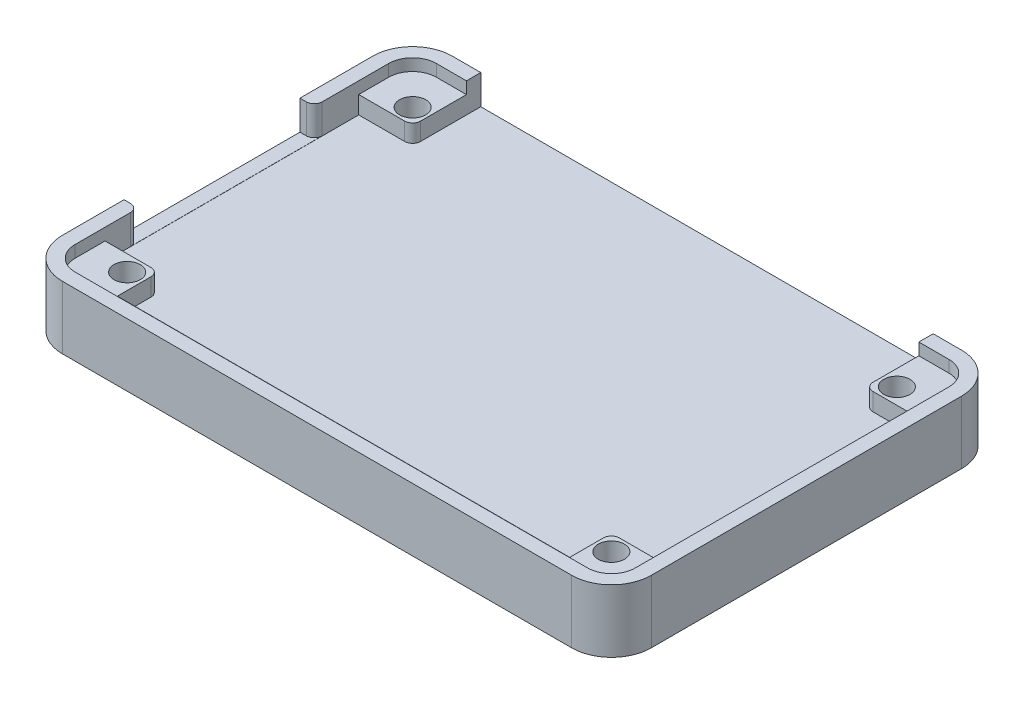
SolidWorks part; units mm, degrees
ref_plane "Front Plane" through (0, 0, 0) normal (0, 0, 1) x (1, 0, 0)
ref_plane "Top Plane" through (0, 0, 0) normal (0, 1, 0) x (1, 0, 0)
ref_plane "Right Plane" through (0, 0, 0) normal (1, 0, 0) x (0, 0, -1)
sketch "Sketch1" plane through (0, 0, 0) normal (0, 1, 0) x (1, 0, 0)
  line L1 (-37, -24.5) -> (37, -24.5)
  line L2 (-37, -24.5) -> (-37, 24.5)
  line L3 (-37, 24.5) -> (37, 24.5)
  line L4 (37, -24.5) -> (37, 24.5)
  line L5 (-37, -24.5) -> (37, 24.5) construction
  line L6 (-37, 24.5) -> (37, -24.5) construction
  point P0 (0, 0)
  dimension "D1" = 74
  dimension "D2" = 49
extrude "Boss-Extrude1" add sketch "Sketch1" along normal blind 7.9
sketch "Sketch3" plane through (0, 7.9, 0) normal (0, 1, 0) x (1, 0, 0)
  line L1 (-30.424, -17.9375) -> (30.424, -17.9375) construction
  line L2 (-30.424, -17.9375) -> (-30.424, 17.9375) construction
  line L3 (-30.424, 17.9375) -> (30.424, 17.9375) construction
  line L4 (30.424, -17.9375) -> (30.424, 17.9375) construction
  line L5 (-30.424, -17.9375) -> (30.424, 17.9375) construction
  line L6 (-30.424, 17.9375) -> (30.424, -17.9375) construction
  circle A0 centre (-30.424, 17.9375) radius 1.65
  circle A1 centre (30.424, 17.9375) radius 1.65
  circle A2 centre (-30.424, -17.9375) radius 1.65
  circle A3 centre (30.424, -17.9375) radius 1.65
  point P0 (0, 0)
  dimension "D3" = 3.3
  dimension "D4" = 3.3
  dimension "D5" = 3.3
  dimension "D6" = 3.3
  dimension "D1" = 60.848
  dimension "D2" = 35.875
fillet "Fillet1" radius 5 4 edges at (-37, 3.95, 24.5) (-37, 3.95, -24.5) (37, 3.95, 24.5) (37, 3.95, -24.5)
sketch "Sketch5" plane through (0, 7.9, 0) normal (0, 1, 0) x (1, 0, 0)
  line L0 (-35.2, 15.9375) -> (-28.424, 15.9375)
  line L1 (-28.424, 15.9375) -> (-28.424, 21.1718)
  line L3 (28.424, 21.1718) -> (28.424, 15.9375)
  line L4 (28.424, 15.9375) -> (35.2, 15.9375)
  line L5 (35.2, 15.9375) -> (35.2, -15.9375)
  line L6 (35.2, -15.9375) -> (28.424, -15.9375)
  line L11 (-35.2, 15.9375) -> (-35.2, -15.9375)
  line L12 (-35.2, -15.9375) -> (-28.424, -15.9375)
  line L14 (37, -19.5) -> (37, 19.5) construction
  line L15 (-37, 19.5) -> (-37, -19.5) construction
  line L17 (-28.424, -15.9375) -> (-28.424, -21.17)
  line L18 (-28.424, -21.17) -> (28.424, -21.17)
  line L19 (28.424, -21.17) -> (28.424, -15.9375)
  line L20 (-32, -24.5) -> (32, -24.5) construction
  line L21 (-28.424, 21.1718) -> (-28.424, 24.5)
  line L22 (32, 24.5) -> (-32, 24.5) construction
  line L23 (-28.424, 24.5) -> (28.424, 24.5)
  line L24 (28.424, 24.5) -> (28.424, 21.1718)
  dimension "D1" = 2
  dimension "D2" = 2
  dimension "D3" = 2
  dimension "D4" = 3.33
  dimension "D6" = 2
  dimension "D7" = 2
  dimension "D8" = 2
  dimension "D9" = 1.8
  dimension "D10" = 1.8
extrude "Cut-Extrude4" cut sketch "Sketch5" against normal blind 3.72
extrude "Cut-Extrude6" cut sketch "Sketch3" against normal blind 7.9
sketch "Sketch7" plane through (-37, 0, 0) normal (-1, 0, 0) x (0, 0, 1)
  line L0 (-10.35, 7.9) -> (-10.35, 4.2)
  line L1 (-19.5, 7.9) -> (19.5, 7.9) construction
  line L2 (-10.35, 4.2) -> (11.75, 4.2)
  line L3 (11.75, 4.2) -> (11.75, 7.9)
  line L4 (11.75, 7.9) -> (-10.35, 7.9)
  line L8 (24.5, 7.9) -> (24.5, 0) construction
  line L9 (-24.5, 0) -> (-24.5, 7.9) construction
  dimension "D1" = 3.7
  dimension "D2" = 12.75
  dimension "D3" = 14.15
  dimension "D4" = 22.1
extrude "Cut-Extrude7" cut sketch "Sketch7" against normal blind 3
sketch "Sketch8" plane through (0, 7.9, 0) normal (0, 1, 0) x (1, 0, 0)
  line L0 (-35.2, 22.7) -> (35.2, 22.7)
  line L1 (35.2, 22.7) -> (35.2, -22.7)
  line L2 (35.2, -22.7) -> (-35.2, -22.7)
  line L3 (-35.2, -22.7) -> (-35.2, 22.7)
  line L6 (-37, 19.5) -> (-37, 10.35) construction
  line L9 (37, -19.5) -> (37, 19.5) construction
  line L11 (32, 24.5) -> (28.424, 24.5) construction
  line L13 (-32, -24.5) -> (32, -24.5) construction
  dimension "D1" = 1.8
  dimension "D2" = 1.8
  dimension "D3" = 1.8
  dimension "D4" = 1.8
extrude "Cut-Extrude8" cut sketch "Sketch8" against normal blind 1.5
fillet "Fillet3" radius 3 4 edges at (-35.2, 7.15, -22.7) (35.2, 7.15, -22.7) (-35.2, 7.15, 22.7) (35.2, 7.15, 22.7)
fillet "Fillet4" radius 1 2 edges at (28.424, 5.29, -15.9375) (-28.424, 5.29, -15.9375)
fillet "Fillet5" radius 1 2 edges at (28.424, 5.29, 15.9375) (-28.424, 5.29, 15.9375)
fillet "Fillet6" radius 1 2 edges at (-35.2, 6.05, -10.35) (-35.2, 6.05, 11.75)
